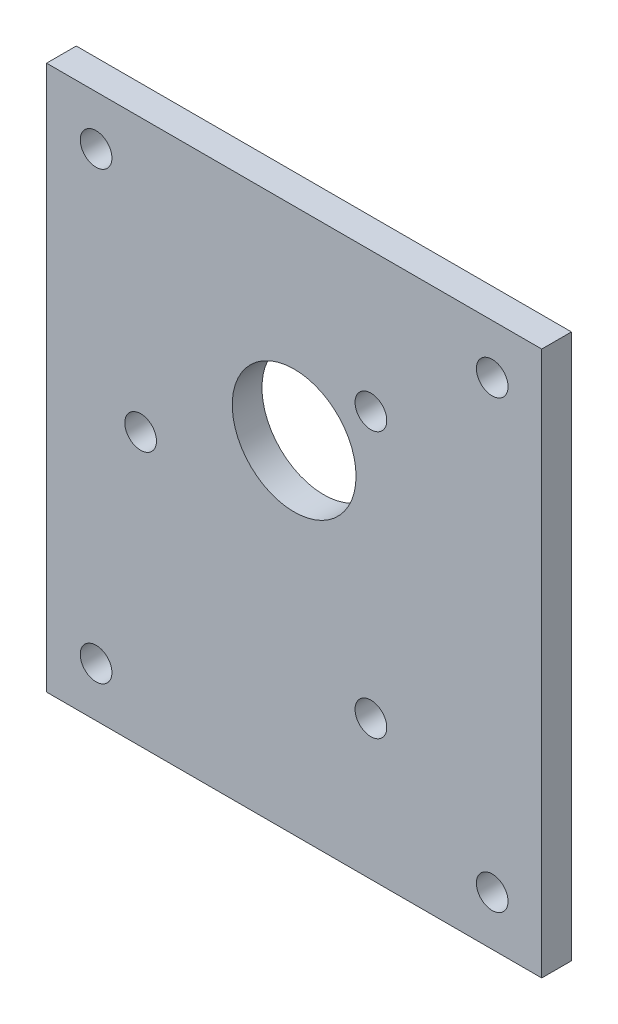
SolidWorks part; units mm, degrees
material "5052-H34"
ref_plane "正面" through (0, 0, 0) normal (0, 0, 1) x (1, 0, 0)
ref_plane "平面" through (0, 0, 0) normal (0, 1, 0) x (1, 0, 0)
ref_plane "右側面" through (0, 0, 0) normal (1, 0, 0) x (0, 0, -1)
sketch "ｽｹｯﾁ1" plane through (0, 0, 0) normal (0, 0, 1) x (1, 0, 0)
  line L0 (0, 0) -> (0, 15.5) construction
  line L1 (-25, 22.5) -> (25, 22.5) construction
  line L2 (-25, 27.5) -> (25, 27.5)
  line L3 (-25, 27.5) -> (-25, -27.5)
  line L4 (-25, -27.5) -> (25, -27.5)
  line L5 (25, 27.5) -> (25, -27.5)
  line L6 (-25, 27.5) -> (25, -27.5) construction
  line L7 (-25, -27.5) -> (25, 27.5) construction
  line L8 (-25, -22.5) -> (25, -22.5) construction
  circle A0 centre (0, 0) radius 15.5 construction
  circle A1 centre (0, 7) radius 6.25
  circle A2 centre (-15.5, 0) radius 1.6
  circle A3 centre (7.75, 13.4234) radius 1.6
  circle A4 centre (7.75, -13.4234) radius 1.6
  circle A5 centre (-20, 22.5) radius 1.6
  circle A6 centre (20, 22.5) radius 1.6
  circle A7 centre (-20, -22.5) radius 1.6
  circle A8 centre (20, -22.5) radius 1.6
  point P15 (0, 0)
  dimension "D1" = 31
  dimension "D2" = 12.5
  dimension "D3" = 7
  dimension "D4" = 3.2
  dimension "D10" = 3.2
  dimension "D11" = 3.2
  dimension "D12" = 3.2
  dimension "D13" = 3.2
  dimension "D17" = 5
  dimension "D6" = 55
  dimension "D7" = 50
  dimension "D8" = 5
  dimension "D9" = 5
  dimension "D14" = 5
  dimension "D15" = 5
  dimension "D16" = 5
  dimension "D5" = 3
extrude "ﾎﾞｽ - 押し出し1" add sketch "ｽｹｯﾁ1" along normal blind 3
